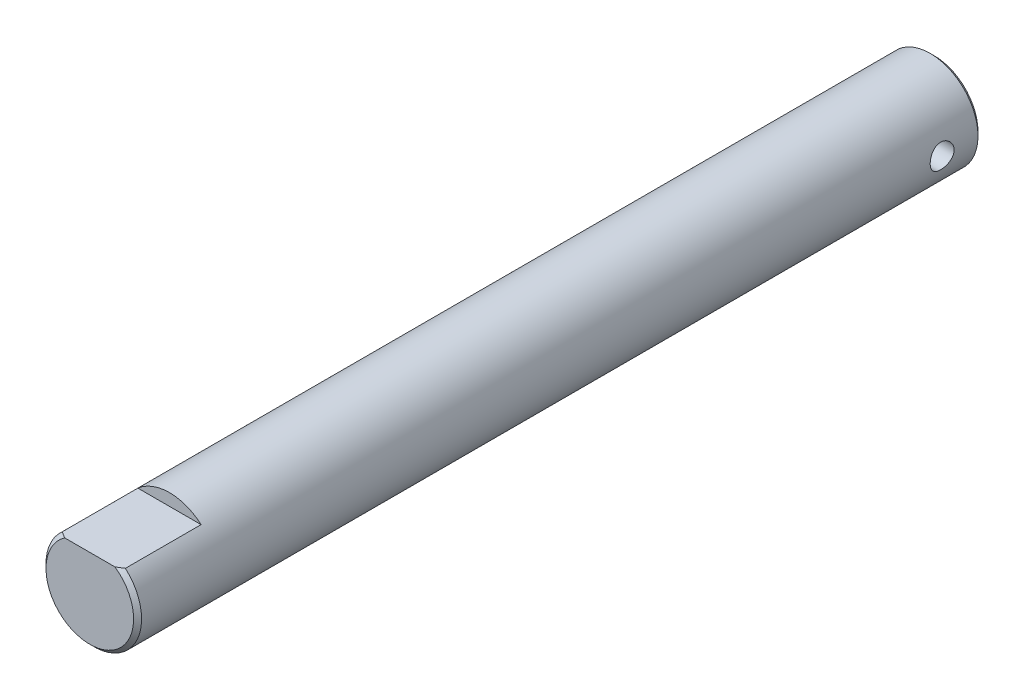
SolidWorks part; units mm, degrees
ref_plane "Front Plane" through (0, 0, 0) normal (0, 0, 1) x (1, 0, 0)
ref_plane "Top Plane" through (0, 0, 0) normal (0, 1, 0) x (1, 0, 0)
ref_plane "Right Plane" through (0, 0, 0) normal (1, 0, 0) x (0, 0, -1)
sketch "Sketch1" plane through (0, 0, 0) normal (0, 0, 1) x (1, 0, 0)
  circle A0 centre (0, 0) radius 6
  dimension "D1" = 12
extrude "Boss-Extrude1" add sketch "Sketch1" along normal blind 106
chamfer "Chamfer1" distance 0.5 angle 45 2 edges at (6, 0, 0) (6, 0, 106)
sketch "Sketch2" plane through (0, 0, 106) normal (0, 0, 1) x (1, 0, 0)
  line L1 (-10, 9.5) -> (10, 9.5)
  line L2 (-10, 9.5) -> (-10, 4.5)
  line L3 (-10, 4.5) -> (10, 4.5)
  line L4 (10, 9.5) -> (10, 4.5)
  point P4 (10, 7)
  dimension "D1" = 4.5
  dimension "D2" = 10
  dimension "D3" = 10
  dimension "D4" = 5
extrude "Cut-Extrude1" cut sketch "Sketch2" against normal blind 10
sketch "Sketch3" plane through (0, 0, 0) normal (1, 0, 0) x (0, 0, -1)
  line L0 (0, -5.5) -> (0, 5.5) construction
  circle A0 centre (-5, 0) radius 1.5
  dimension "D1" = 3
  dimension "D2" = 5
extrude "Cut-Extrude2" cut sketch "Sketch3" against normal through all both and the other way through all
